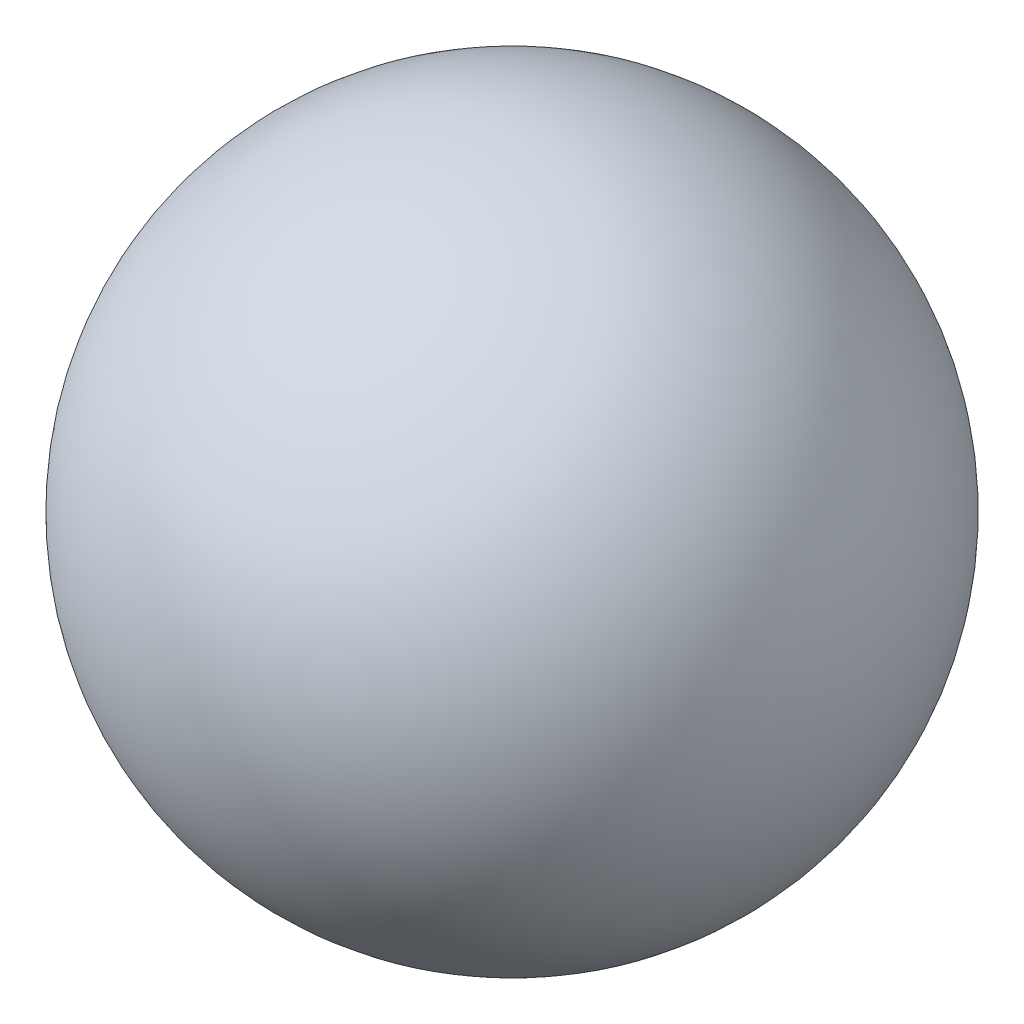
SolidWorks part; units mm, degrees
ref_plane "前视基准面" through (0, 0, 0) normal (0, 0, 1) x (1, 0, 0)
ref_plane "上视基准面" through (0, 0, 0) normal (0, 1, 0) x (1, 0, 0)
ref_plane "右视基准面" through (0, 0, 0) normal (1, 0, 0) x (0, 0, -1)
sketch "草图1" plane through (0, 0, 0) normal (0, 0, 1) x (1, 0, 0)
  line L0 (0, 20) -> (0, -20)
  arc A0 (0, -20) -> (0, 20) centre (0, 0) ccw
revolve "旋转1" add sketch "草图1" angle 360 about L0
